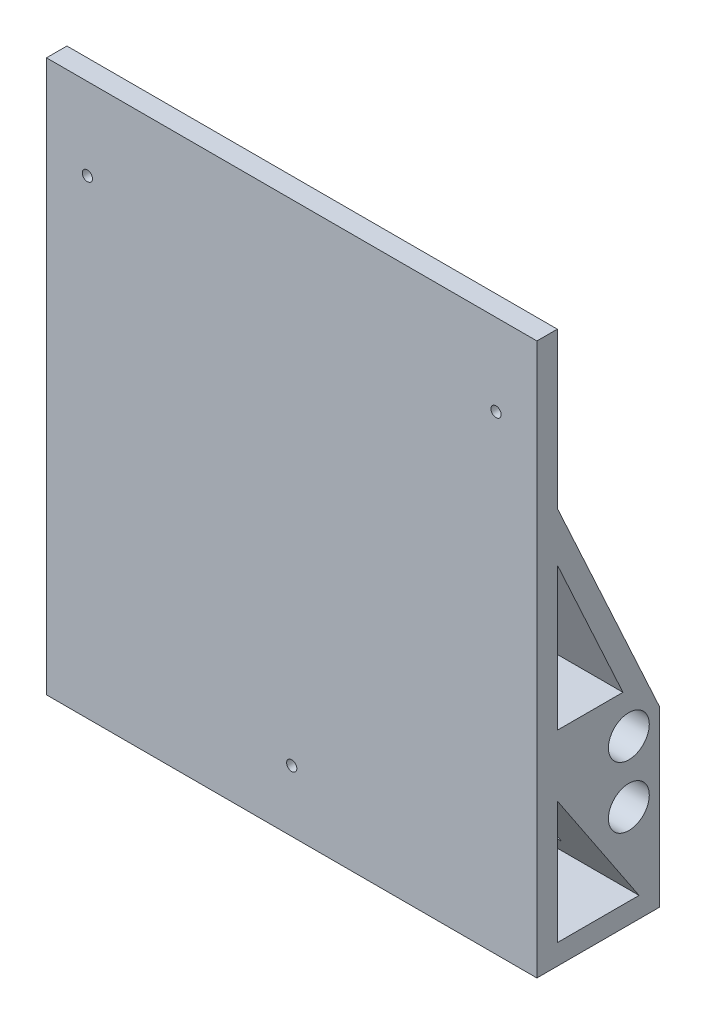
SolidWorks part; units mm, degrees
ref_plane "Front Plane" through (0, 0, 0) normal (0, 0, 1) x (1, 0, 0)
ref_plane "Top Plane" through (0, 0, 0) normal (0, 1, 0) x (1, 0, 0)
ref_plane "Right Plane" through (0, 0, 0) normal (1, 0, 0) x (0, 0, -1)
sketch "Sketch1" plane through (0, 0, 0) normal (1, 0, 0) x (0, 0, -1)
  line L0 (0, 0) -> (0, 135)
  line L1 (0, 0) -> (30, 0)
  line L3 (25, 5) -> (5, 35)
  line L4 (5, 5) -> (5, 35)
  line L5 (5, 5) -> (25, 5)
  line L6 (30, 0) -> (30, 42.5)
  line L8 (0, 135) -> (5, 135)
  line L11 (30, 42.5) -> (5, 97)
  line L12 (5, 97) -> (5, 135)
  circle A0 centre (22.5, 40) radius 5
  circle A1 centre (22.5, 25) radius 5
  dimension "D12" = 10
  dimension "D15" = 10
  dimension "D1" = 135
  dimension "D2" = 30
  dimension "D3" = 5
  dimension "D4" = 5
  dimension "D5" = 20
  dimension "D6" = 0
  dimension "D7" = 35
  dimension "D8" = 42.5
  dimension "D9" = 38
  dimension "D10" = 54.5
  dimension "D11" = 59.9604
  dimension "D13" = 40
  dimension "D14" = 22.5
  dimension "D16" = 25
  dimension "D17" = 15
extrude "Boss-Extrude1" add sketch "Sketch1" against normal blind 120
sketch "Sketch2" plane through (0, 0, -30) normal (0, 0, -1) x (-1, 0, 0)
  circle A0 centre (60, 3.75) radius 3.75
  dimension "D1" = 7.5
  dimension "D2" = 3.75
  dimension "D3" = 60
extrude "Boss-Extrude2" add sketch "Sketch2" along normal blind 20
sketch "Sketch3" plane through (0, 0, -30) normal (0, 0, -1) x (-1, 0, 0)
  circle A0 centre (60, 52.25) radius 3.75
  circle A1 centre (60, 3.75) radius 3.75 construction
  point P2 (0, 0)
  dimension "D1" = 7.5
  dimension "D2" = 60
  dimension "D3" = 48.5
extrude "Boss-Extrude3" add sketch "Sketch3" along normal blind 20 and the other way blind 15
sketch "Sketch4" plane through (0, 0, 0) normal (0, 0, 1) x (1, 0, 0)
  circle A0 centre (-60, 15) radius 1.25
  point P2 (0, 0)
  dimension "D2" = 2.5
  dimension "D1" = 60
  dimension "D3" = 15
extrude "Cut-Extrude1" cut sketch "Sketch4" against normal blind 50
sketch "Sketch5" plane through (0, 0, -30) normal (0, 0, -1) x (-1, 0, 0)
  line L0 (15, 36) -> (15, 11)
  line L1 (15, 11) -> (105, 11)
  line L2 (105, 11) -> (105, 36)
  line L3 (105, 36) -> (15, 36)
  dimension "D1" = 15
  dimension "D2" = 15
  dimension "D3" = 25
  dimension "D4" = 1
extrude "Cut-Extrude5" cut sketch "Sketch5" along direction (0, 0, 1) on the side against the normal blind 25
sketch "Sketch6" plane through (-15, 0, 0) normal (-1, 0, 0) x (0, 0, 1)
  circle A0 centre (-22.5, 25) radius 5
extrude "Boss-Extrude4" add sketch "Sketch6" against normal blind 5
sketch "Sketch7" plane through (-105, 0, 0) normal (1, 0, 0) x (0, 0, -1)
  circle A0 centre (22.5, 25) radius 5
extrude "Boss-Extrude5" add sketch "Sketch7" against normal blind 5
ref_plane "Plane1" through (-15, 0, 0) normal (-1, 0, 0) x (0, 0, 1)
sketch "Sketch8" plane through (-15, 0, 0) normal (-1, 0, 0) x (0, 0, 1)
  circle A0 centre (-22.5, 40) radius 5
extrude "Boss-Extrude6" add sketch "Sketch8" along normal blind 95 and the other way blind 5
sketch "Sketch9" plane through (0, 36, 0) normal (0, -1, 0) x (1, 0, 0)
  line L1 (-105, -5) -> (-15, -5)
  line L2 (-105, -5) -> (-105, -30)
  line L3 (-105, -30) -> (-15, -30)
  line L4 (-15, -5) -> (-15, -30)
extrude "Boss-Extrude7" add sketch "Sketch9" along normal blind 2.5
sketch "Sketch10" plane through (0, 0, 0) normal (0, 0, 1) x (1, 0, 0)
  line L0 (-120, 135) -> (-120, 0) construction
  line L1 (-120, 0) -> (0, 0) construction
  line L2 (-60, 0) -> (-60, 135) construction
  line L3 (-120, 135) -> (0, 135) construction
  circle A0 centre (-110, 115) radius 1.25
  circle A1 centre (-60, 15) radius 1.25 construction
  circle A2 centre (-10, 115) radius 1.25
  dimension "D1" = 20
  dimension "D2" = 10
extrude "Cut-Extrude6" cut sketch "Sketch10" against normal blind 22.5
sketch "Sketch11" plane through (0, 0, 0) normal (1, 0, 0) x (0, 0, -1)
  line L0 (5, 85.0079) -> (5, 50.0079)
  line L1 (5, 50.0079) -> (21.055, 50.0079)
  line L2 (21.055, 50.0079) -> (5, 85.0079)
  line L3 (5, 97) -> (5, 135) construction
  line L5 (30, 42.5) -> (5, 97) construction
  dimension "D1" = 35
  dimension "D2" = 5
extrude "Cut-Extrude7" cut sketch "Sketch11" against normal blind 120
